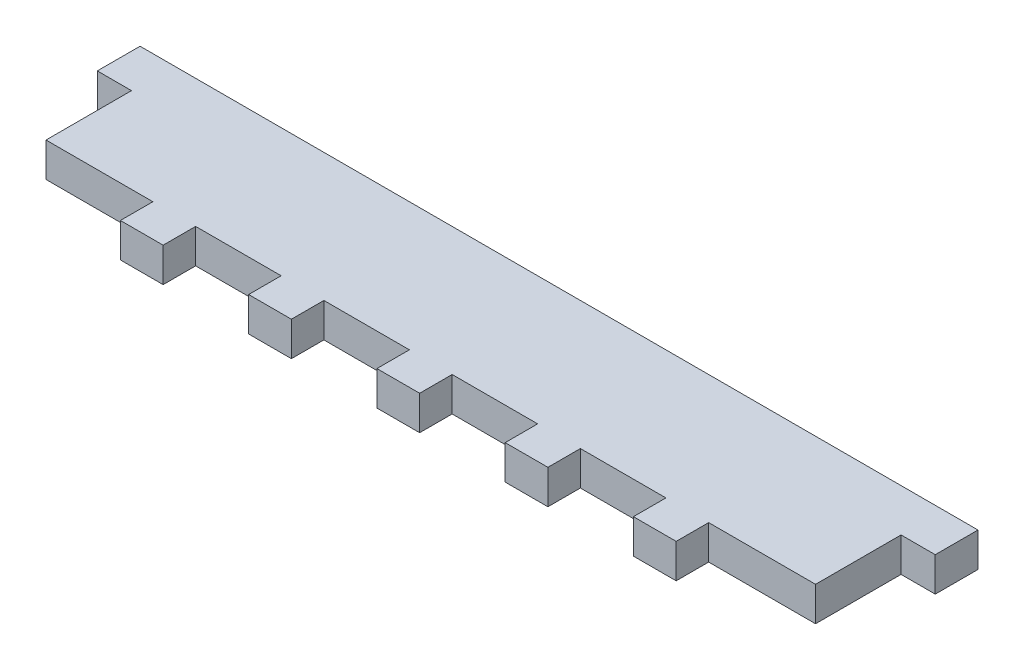
SolidWorks part; units mm, degrees
ref_plane "Front Plane" through (0, 0, 0) normal (0, 0, 1) x (1, 0, 0)
ref_plane "Top Plane" through (0, 0, 0) normal (0, 1, 0) x (1, 0, 0)
ref_plane "Right Plane" through (0, 0, 0) normal (1, 0, 0) x (0, 0, -1)
sketch "Sketch1" plane through (0, 0, 0) normal (0, 1, 0) x (1, 0, 0)
  line L1 (0, 0) -> (114.3, 0)
  line L2 (0, 0) -> (0, 12.7)
  line L3 (0, 19.05) -> (114.3, 19.05)
  line L4 (114.3, 0) -> (114.3, 12.7)
  line L5 (0, 19.05) -> (-5.08, 19.05)
  line L7 (0, 12.7) -> (-5.08, 12.7)
  line L8 (-5.08, 19.05) -> (-5.08, 12.7)
  line L9 (114.3, 19.05) -> (119.38, 19.05)
  line L11 (114.3, 12.7) -> (119.38, 12.7)
  line L12 (119.38, 19.05) -> (119.38, 12.7)
  dimension "D1" = 114.3
  dimension "D2" = 19.05
  dimension "D3" = 5.08
  dimension "D4" = 6.35
extrude "Boss-Extrude1" add sketch "Sketch1" along normal blind 5.08
sketch "Sketch2" plane through (0, 0, 0) normal (0, 0, 1) x (1, 0, 0)
  line L0 (0, 5.08) -> (114.3, 5.08) construction
  line L1 (15.875, 5.08) -> (22.225, 5.08)
  line L2 (15.875, 5.08) -> (15.875, 0)
  line L3 (15.875, 0) -> (22.225, 0)
  line L4 (22.225, 5.08) -> (22.225, 0)
  line L5 (0, 0) -> (114.3, 0) construction
  line L6 (0, 5.08) -> (0, 0) construction
  dimension "D1" = 6.35
  dimension "D2" = 15.875
extrude "Boss-Extrude2" add sketch "Sketch2" along normal blind 4.826
pattern_linear "LPattern1" count 5 spacing 19.05 along (1, 0, 0) of "Boss-Extrude2"
